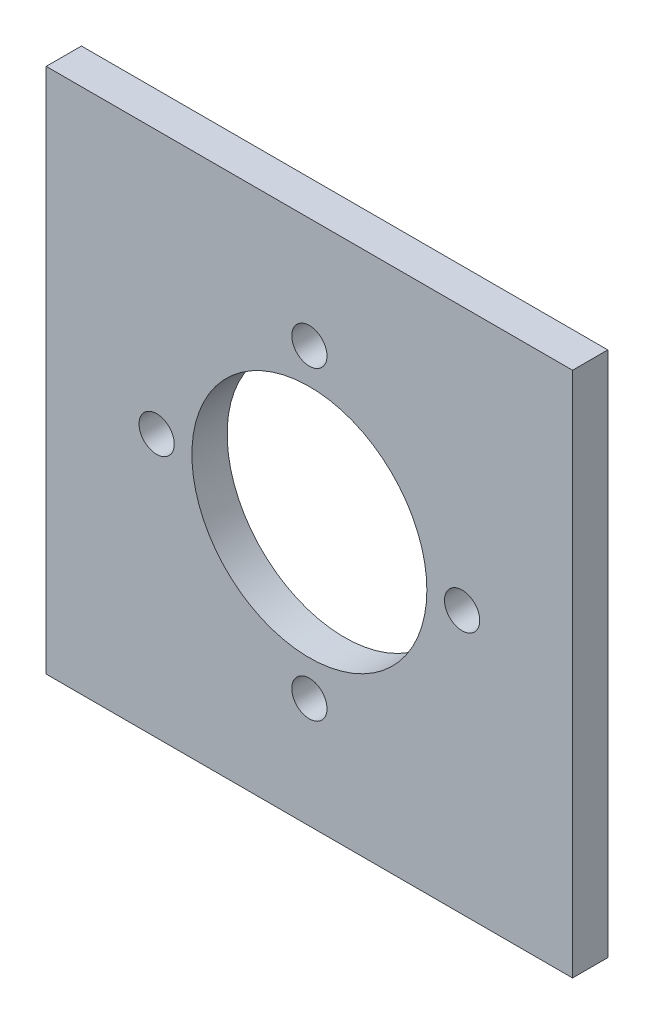
SolidWorks part; units mm, degrees
ref_plane "Plan de face" through (0, 0, 0) normal (0, 0, 1) x (1, 0, 0)
ref_plane "Plan de dessus" through (0, 0, 0) normal (0, 1, 0) x (1, 0, 0)
ref_plane "Plan de droite" through (0, 0, 0) normal (1, 0, 0) x (0, 0, -1)
sketch "Esquisse1" plane through (0, 0, 0) normal (0, 0, 1) x (1, 0, 0)
  line L1 (-35.6819, 22.1053) -> (9.1181, 22.1053)
  line L2 (-35.6819, 22.1053) -> (-35.6819, -22.6947)
  line L3 (-35.6819, -22.6947) -> (9.1181, -22.6947)
  line L4 (9.1181, 22.1053) -> (9.1181, -22.6947)
  dimension "D1" = 44.8
  dimension "D2" = 44.8
extrude "Boss.-Extru.1" add sketch "Esquisse1" along normal blind 3
sketch "Esquisse2" plane through (0, 0, 3) normal (0, 0, 1) x (1, 0, 0)
  line L0 (-35.6819, 22.1053) -> (9.1181, -22.6947) construction
  line L1 (-35.6819, -22.6947) -> (9.1181, 22.1053) construction
  line L2 (-13.2819, -0.2947) -> (-13.2819, 22.1053) construction
  line L3 (9.1181, 22.1053) -> (-35.6819, 22.1053) construction
  circle A0 centre (-13.2819, 12.7053) radius 1.5
  circle A1 centre (-0.2819, -0.2947) radius 1.5
  circle A2 centre (-13.2819, -13.2947) radius 1.5
  circle A3 centre (-26.2819, -0.2947) radius 1.5
  circle A4 centre (-13.2819, -0.2947) radius 10
  point P10 (-13.2819, -0.2947)
  dimension "D2" = 4
  dimension "D1" = 13
extrude "Enlèv. mat.-Extru.1" cut sketch "Esquisse2" against normal blind 3
